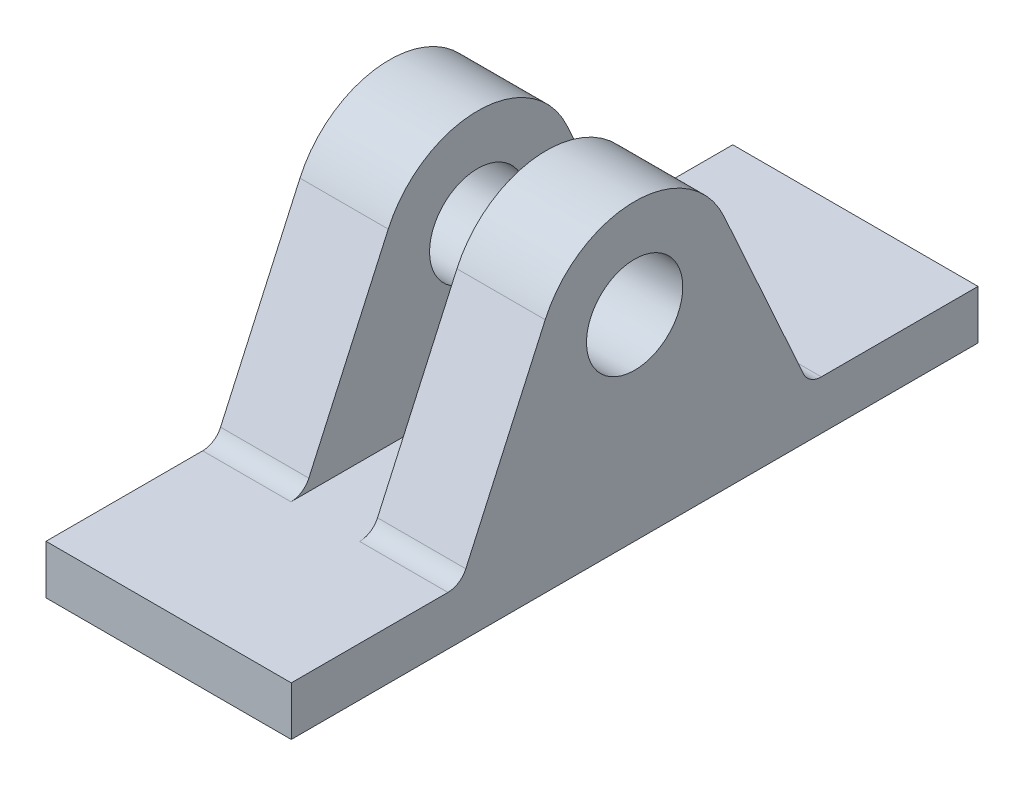
SolidWorks part; units mm, degrees
material "6061-T6 (SS)"
ref_plane "Front Plane" through (0, 0, 0) normal (0, 0, 1) x (1, 0, 0)
ref_plane "Top Plane" through (0, 0, 0) normal (0, 1, 0) x (1, 0, 0)
ref_plane "Right Plane" through (0, 0, 0) normal (1, 0, 0) x (0, 0, -1)
sketch "Sketch1" plane through (0, 0, 0) normal (1, 0, 0) x (0, 0, -1)
  line L0 (22.5949, 7.8452) -> (32.8741, 30.6238)
  line L1 (0, 0) -> (88.9, 0)
  line L2 (0, 0) -> (0, 6.35)
  line L3 (0, 6.35) -> (20.2798, 6.35)
  line L4 (88.9, 0) -> (88.9, 6.35)
  line L5 (56.0259, 30.6238) -> (66.3051, 7.8452)
  line L6 (68.6202, 6.35) -> (88.9, 6.35)
  arc A0 (56.0259, 30.6238) -> (32.8741, 30.6238) centre (44.45, 25.4) ccw
  arc A1 (20.2798, 6.35) -> (22.5949, 7.8452) centre (20.2798, 8.89) ccw
  arc A2 (66.3051, 7.8452) -> (68.6202, 6.35) centre (68.6202, 8.89) ccw
  circle A3 centre (44.45, 25.4) radius 6.2294
  dimension "D3" = 25.4
  dimension "D7" = 5.08
  dimension "D8" = 5.08
  dimension "D9" = 12.4587
  dimension "D1" = 88.9
  dimension "D2" = 6.35
  dimension "D4" = 25.4
extrude "Boss-Extrude1" add sketch "Sketch1" against normal blind 31.75
sketch "Sketch2" plane through (0, 0, 0) normal (0, 0, 1) x (1, 0, 0)
  line L0 (-31.75, 6.35) -> (0, 6.35) construction
  line L1 (-20.32, 6.35) -> (-11.43, 6.35)
  line L2 (-20.32, 6.35) -> (-20.32, 38.1)
  line L3 (-20.32, 38.1) -> (-11.43, 38.1)
  line L4 (-11.43, 6.35) -> (-11.43, 38.1)
  line L5 (0, 38.1) -> (-31.75, 38.1) construction
  line L6 (-31.75, 6.35) -> (0, 6.35) construction
  point P8 (-15.875, 6.35)
  point P11 (-15.875, 6.35)
  dimension "D1" = 8.89
extrude "Cut-Extrude1" cut sketch "Sketch2" against normal through all
